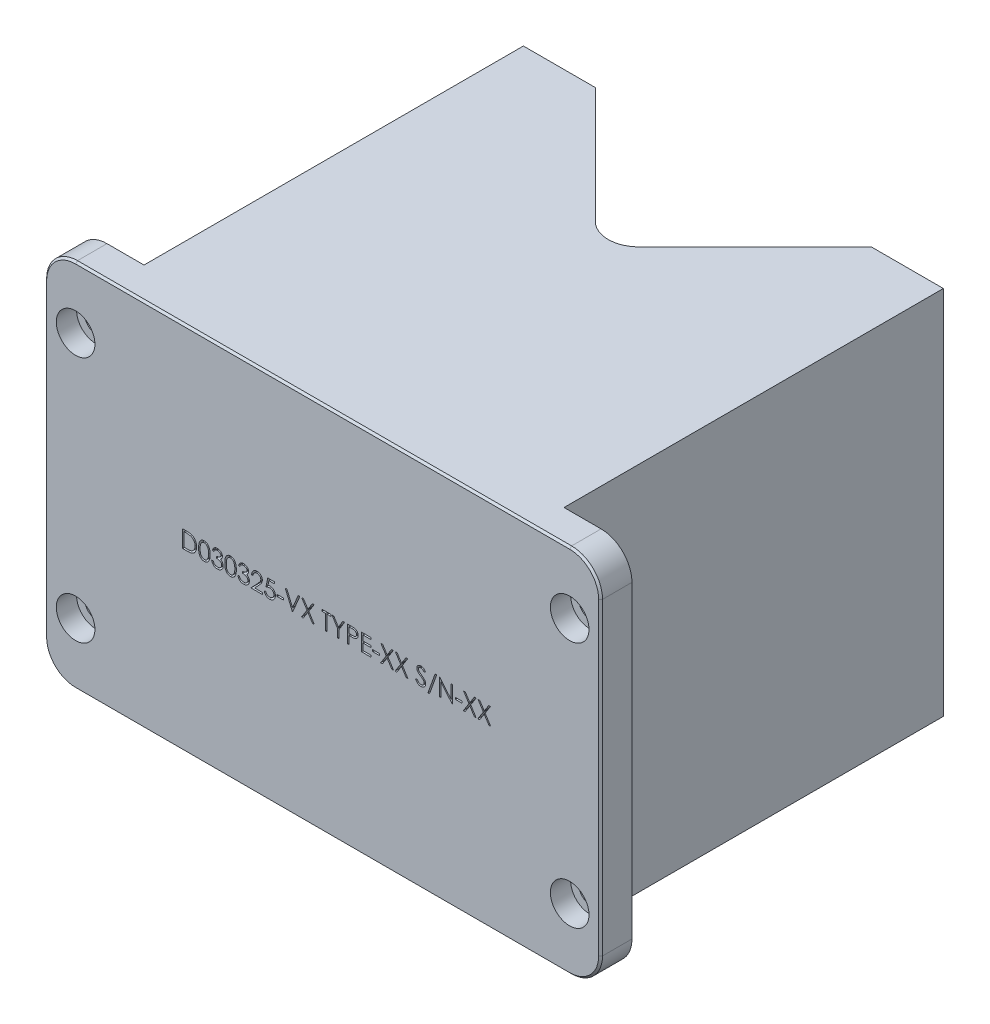
SolidWorks part; units mm, degrees
material "6061-T6 Al"
ref_plane "Front" through (0, 0, 0) normal (0, 0, 1) x (1, 0, 0)
ref_plane "Top" through (0, 0, 0) normal (0, 1, 0) x (1, 0, 0)
ref_plane "Right" through (0, 0, 0) normal (1, 0, 0) x (0, 0, -1)
sketch "Sketch1" plane through (0, 0, 0) normal (0, 0, 1) x (1, 0, 0)
  line L0 (0, 33.4252) -> (0, 0) construction
  line L1 (-57.15, 0) -> (-57.15, 76.2)
  line L2 (-57.15, 0) -> (57.15, 0)
  line L4 (-57.15, 76.2) -> (57.15, 76.2)
  line L5 (57.15, 0) -> (57.15, 76.2)
  dimension "D1" = 76.2
  dimension "D2" = 114.3
extrude "Extrude1" add sketch "Sketch1" along normal blind 9.525
sketch "Sketch2" plane through (0, 76.2, 0) normal (0, 1, 0) x (-1, 0, 0)
  line L0 (0, 0) -> (0, -101.6) construction
  line L1 (-43.18, 0) -> (-43.18, -101.6)
  line L3 (-57.15, 0) -> (57.15, 0) construction
  line L4 (-43.18, -101.6) -> (43.18, -101.6)
  line L5 (43.18, 0) -> (43.18, -101.6)
  line L6 (-43.18, 0) -> (43.18, 0)
  dimension "D1" = 43.18
  dimension "D2" = 101.6
extrude "Extrude7" add sketch "Sketch2" against normal through all
sketch "Sketch3" plane through (0, 76.2, 0) normal (0, 1, 0) x (-1, 0, 0)
  circle A0 centre (0.0096, -97.9035) radius 40.513
  circle A1 centre (0.0096, -97.9035) radius 38.1 construction
  dimension "D1" = 81.026
hole_wizard "CBORE for #8 Socket Head Cap Screw1" positions "Sketch5" profile "Sketch4" counterbore size "#8" standard "Ansi Inch"
sketch "Sketch5" plane through (0, 0, 9.525) normal (0, 0, 1) x (1, 0, 0)
  line L0 (57.15, 76.2) -> (-57.15, 76.2) construction
  line L1 (-57.15, 76.2) -> (-57.15, 0) construction
  point P0 (-50.8, 63.5)
  dimension "D1" = 12.7
  dimension "D2" = 6.35
sketch "Sketch4" plane through (-50.8, 63.5, 9.525) normal (1, 0, 0) x (0, -1, 0)
  line L0 (0, 0) -> (0, 26.7507)
  line L1 (0, 26.7507) -> (2.2479, 25.4)
  line L2 (2.2479, 25.4) -> (2.2479, 4.1656)
  line L3 (2.2479, 4.1656) -> (3.9687, 4.1656)
  line L4 (3.9687, 4.1656) -> (3.9687, 0)
  line L5 (3.9687, 0) -> (0, 0)
  line L10 (0, 26.7507) -> (-2.2479, 25.4) construction
  line L11 (0, -6.35) -> (0, 107.95) construction
  dimension "Hole Dia." = 4.4958
  dimension "Hole Depth" = 25.4
  dimension "C'Bore Dia." = 7.9375
  dimension "C'Bore Depth" = 4.1656
  dimension "Drill Angle" = 118
pattern_linear "LPattern1" count 2 spacing 50.8 along (0, -1, 0) count 2 spacing 101.6 along (1, 0, 0) of "CBORE for #8 Socket Head Cap Screw1"
fillet "Fillet1" radius 6.35 4 edges at (57.15, 0, 4.7625) (57.15, 76.2, 4.7625) (-57.15, 0, 4.7625) (-57.15, 76.2, 4.7625)
sketch "Sketch6" plane through (0, 0, 0) normal (0, -1, 0) x (1, 0, 0)
  line L0 (-50.8, 5.3594) -> (-50.8, 9.525) construction
  line L1 (-50.8, -74.93) -> (52.3756, -74.93)
  line L2 (-50.8, -74.93) -> (-50.8, -105.873)
  line L3 (-50.8, -105.873) -> (52.3756, -105.873)
  line L4 (52.3756, -74.93) -> (52.3756, -105.873)
  line L5 (-50.8, 9.525) -> (50.8, 9.525) construction
  dimension "D1" = 84.455
extrude "Cut-Extrude2" cut sketch "Sketch6" against normal through all
sketch "Sketch11" plane through (0, 0, 9.525) normal (0, 0, 1) x (1, 0, 0)
  text T0 "D030325-VX TYPE-XX S/N-XX"
extrude "Cut-Extrude3" cut sketch "Sketch11" against normal blind 2.54
chamfer "Chamfer1" distance 0.3969 angle 45 8 edges at (-55.2901, 1.8599, 9.525) (-57.15, 38.1, 9.525) (-55.2901, 74.3401, 9.525) (0, 76.2, 9.525) (55.2901, 74.3401, 9.525) (57.15, 38.1, 9.525) (55.2901, 1.8599, 9.525) (0, 0, 9.525)
chamfer "Chamfer2" distance 0.3969 angle 45 10 edges at (-55.2901, 1.8599, 0) (-57.15, 38.1, 0) (-55.2901, 74.3401, 0) (55.2901, 74.3401, 0) (57.15, 38.1, 0) (55.2901, 1.8599, 0)
sketch "Sketch12" plane through (0, 76.2, 0) normal (0, 1, 0) x (-1, 0, 0)
  line L0 (0, -49.6437) -> (0, 0) construction
  line L2 (-43.18, -74.93) -> (43.18, -74.93) construction
  line L3 (-28.3678, -74.93) -> (28.3678, -74.93)
  line L5 (4.4901, -51.0523) -> (28.3678, -74.93)
  line L11 (-4.4901, -51.0523) -> (-28.3678, -74.93)
  arc A2 (-4.4901, -51.0523) -> (4.4901, -51.0523) centre (0, -55.5424) cw
  dimension "D1" = 6.35
  dimension "D2" = 19.3876
  dimension "D4" = 90
  dimension "D3" = 45
extrude "Cut-Extrude4" cut sketch "Sketch12" against normal blind 104.14
sketch "Sketch14" plane through (0, 0, 0) normal (0, 0, -1) x (-1, 0, 0)
  line L0 (-50.8, 76.2) -> (-43.18, 76.2) construction
  line L1 (-50.8, 76.2) -> (-43.18, 76.2)
  line L2 (-43.18, 76.2) -> (-43.18, 0) construction
  line L3 (-43.18, 76.2) -> (-43.18, 0)
  line L4 (-57.15, 6.35) -> (-57.15, 69.85) construction
  line L5 (-57.15, 6.35) -> (-57.15, 69.85)
  line L6 (-43.18, 0) -> (-50.8, 0) construction
  line L7 (-43.18, 0) -> (-50.8, 0)
  arc A1 (-50.8, 76.2) -> (-57.15, 69.85) centre (-50.8, 69.85) ccw construction
  arc A2 (-50.8, 76.2) -> (-57.15, 69.85) centre (-50.8, 69.85) ccw
  arc A3 (-57.15, 6.35) -> (-50.8, 0) centre (-50.8, 6.35) ccw construction
  arc A4 (-57.15, 6.35) -> (-50.8, 0) centre (-50.8, 6.35) ccw
extrude "Cut-Extrude5" cut sketch "Sketch14" against normal blind 3.0734
sketch "Sketch15" plane through (0, 0, 0) normal (0, 0, -1) x (-1, 0, 0)
  line L0 (43.18, 0) -> (43.18, 76.2) construction
  line L1 (43.18, 0) -> (43.18, 76.2)
  line L2 (43.18, 76.2) -> (50.8, 76.2) construction
  line L3 (43.18, 76.2) -> (50.8, 76.2)
  line L4 (57.15, 69.85) -> (57.15, 6.35) construction
  line L5 (57.15, 69.85) -> (57.15, 6.35)
  line L6 (50.8, 0) -> (43.18, 0) construction
  line L7 (50.8, 0) -> (43.18, 0)
  arc A0 (57.15, 69.85) -> (50.8, 76.2) centre (50.8, 69.85) ccw construction
  arc A1 (57.15, 69.85) -> (50.8, 76.2) centre (50.8, 69.85) ccw
  arc A2 (50.8, 0) -> (57.15, 6.35) centre (50.8, 6.35) ccw construction
  arc A3 (50.8, 0) -> (57.15, 6.35) centre (50.8, 6.35) ccw
extrude "Cut-Extrude6" cut sketch "Sketch15" against normal blind 3.0734
